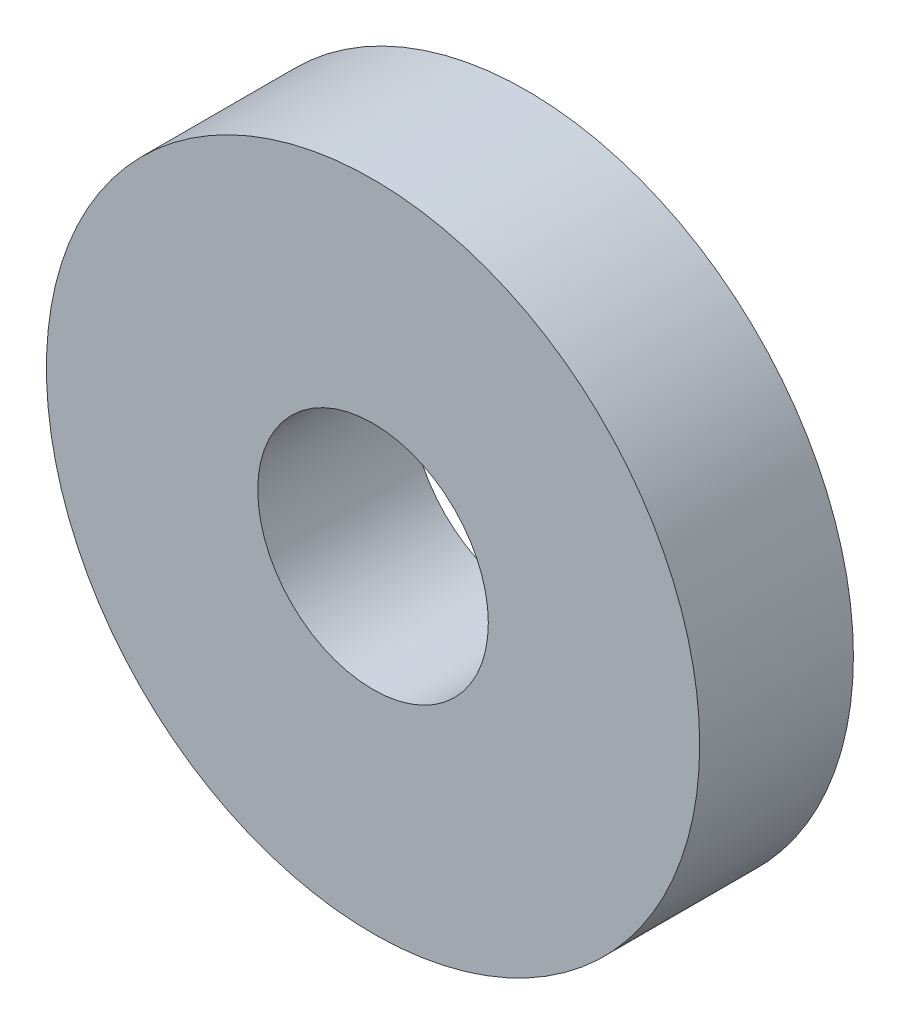
SolidWorks part; units mm, degrees
ref_plane "Front Plane" through (0, 0, 0) normal (0, 0, 1) x (1, 0, 0)
ref_plane "Top Plane" through (0, 0, 0) normal (0, 1, 0) x (1, 0, 0)
ref_plane "Right Plane" through (0, 0, 0) normal (1, 0, 0) x (0, 0, -1)
sketch "Sketch1" plane through (0, 0, 0) normal (0, 0, 1) x (1, 0, 0)
  circle A0 centre (0, 0) radius 3
  circle A1 centre (0, 0) radius 8.5
  dimension "D1" = 17
  dimension "D2" = 6
extrude "Boss-Extrude1" add sketch "Sketch1" along normal blind 4
